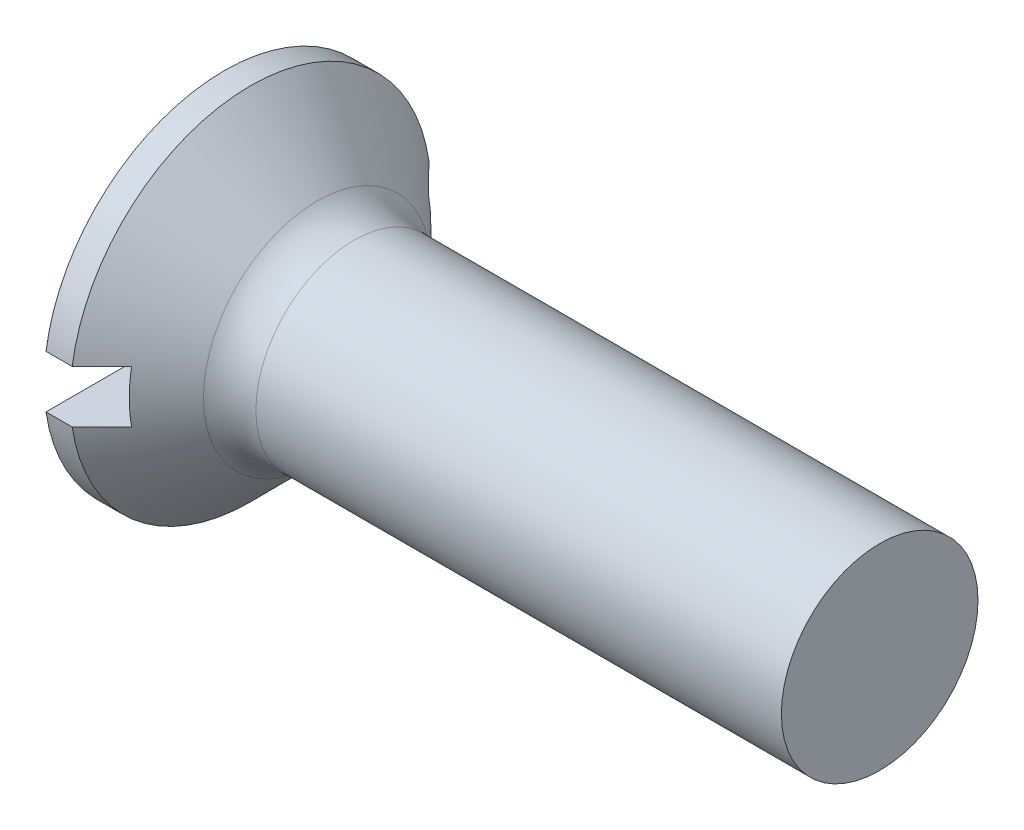
SolidWorks part; units mm, degrees
ref_plane "Plane1" through (0, 0, 0) normal (0, 0, 1) x (1, 0, 0)
ref_plane "Plane2" through (0, 0, 0) normal (0, 1, 0) x (1, 0, 0)
ref_plane "Plane3" through (0, 0, 0) normal (1, 0, 0) x (0, 0, -1)
sketch "BodySke" plane through (0, 0, 0) normal (0, 0, 1) x (1, 0, 0)
  line L0 (0, 0) -> (0, 2.75)
  line L1 (0, 2.75) -> (0.4, 2.75)
  line L2 (1.65, 1.5) -> (10, 1.5)
  line L3 (10, 1.5) -> (10, 0)
  line L4 (10, 0) -> (0, 0)
  line L5 (-6.35, 0) -> (82.55, 0) construction
  line L6 (1.65, -1.5) -> (10, -1.5) construction
  line L7 (0.4, -2.75) -> (1.65, -1.5) construction
  line L8 (0.4, 2.75) -> (1.65, 1.5)
  line L9 (0, -2.75) -> (0.4, -2.75) construction
  line L10 (2.15, 3.0875) -> (2.15, -6.4375) construction
  line L11 (0, 6.35) -> (0, -3.175) construction
  dimension "Diameter" = 3
  dimension "Length" = 10
  dimension "Head_ht" = 1.65
  dimension "Head_dia" = 5.5
  dimension "Head_ang" = 90
  dimension "D6" = 0.4
  dimension "Advance" = 0.5
  dimension "Thread_nom" = 10
revolve "Base-Revolve" add sketch "BodySke" angle 360 about L5
cosmetic thread "ThreadCosmetic" parameters "Thread_length"=7.85, "Thread_minor"=2.439
fillet "Fillet1" radius 0.8 1 edges at (1.65, 0, 1.5)
sketch "Sketch2" plane through (0, 0, 0) normal (-1, 0, 0) x (0, 0, 1)
  line L0 (-2.75, -0.4) -> (2.75, -0.4)
  line L1 (-2.75, -0.4) -> (-2.75, 0.4)
  line L2 (2.75, 0.4) -> (-2.75, 0.4)
  line L3 (2.75, 0.4) -> (2.75, -0.4)
  dimension "D1" = 0.4
  dimension "Slot_width" = 0.8
  dimension "D2" = 5.5
  dimension "D3" = 2.75
extrude "Slot" cut sketch "Sketch2" against normal blind 0.85
sketch "ThdSchSke" plane through (0, 0, 0) normal (0, 0, 1) x (1, 0, 0)
  line L0 (2.15, -1.2195) -> (1.9536, -1.5)
  line L1 (2.15, -1.2195) -> (2.3464, -1.5)
  line L2 (2.3464, -1.5) -> (2.3464, -1.875)
  line L3 (-3.175, 0) -> (5.1513, 0) construction
  line L5 (2.3464, -1.875) -> (1.9536, -1.875)
  line L6 (1.9536, -1.875) -> (1.9536, -1.5)
  line L7 (0, 2.75) -> (0, 0.4) construction
  dimension "Thread_minor" = 2.439
  dimension "Diameter" = 3
  dimension "Start" = 2.15
  dimension "SideAngle" = 55
  dimension "VeeAngle" = 70
  dimension "Overcut" = 3.75
revolve "ThreadSchematic" [suppressed] cut sketch "ThdSchSke" angle 360 about L3
pattern_linear "ThdSchPat" [suppressed]
equation "\"D1@Sketch2\" = \"Slot_width@Sketch2\" / 2"
equation "\"D2@Sketch2\" = \"Head_dia@BodySke\""
equation "\"D3@Sketch2\" = \"D2@Sketch2\" / 2"
equation "\"Thread_length@ThreadCosmetic\" = ((sgn( (\"Length@BodySke\" - \"Advance@BodySke\" * 1.0 - \"Head_ht@BodySke\" ) - \"Thread_nom@BodySke\" )-1)*( (\"Length@BodySke\" - \"Advance@BodySke\" * 1.0 - \"Head_ht@BodySke\" ) - \"Thread_nom@BodySke\" ))/-2+ \"Thread_nom@BodySke\""
equation "\"Thread_minor@ThdSchSke\" = \"Thread_minor@ThreadCosmetic\""
equation "\"Diameter@ThdSchSke\" = \"Diameter@BodySke\""
equation "\"Overcut@ThdSchSke\" = \"Diameter@BodySke\" * 1.25"
equation "\"Start@ThdSchSke\" = 0.000001 + \"Length@BodySke\" - \"Thread_length@ThreadCosmetic\"  '---Countersunk---"
equation "\"Num_threads@ThdSchPat\" = int( \"Thread_length@ThreadCosmetic\" / \"Advance@BodySke\" + 0.999 )  + 1"
equation "\"Advance@ThdSchPat\" = \"Thread_length@ThreadCosmetic\" /  (\"Num_threads@ThdSchPat\" - 1) 'relax it"
